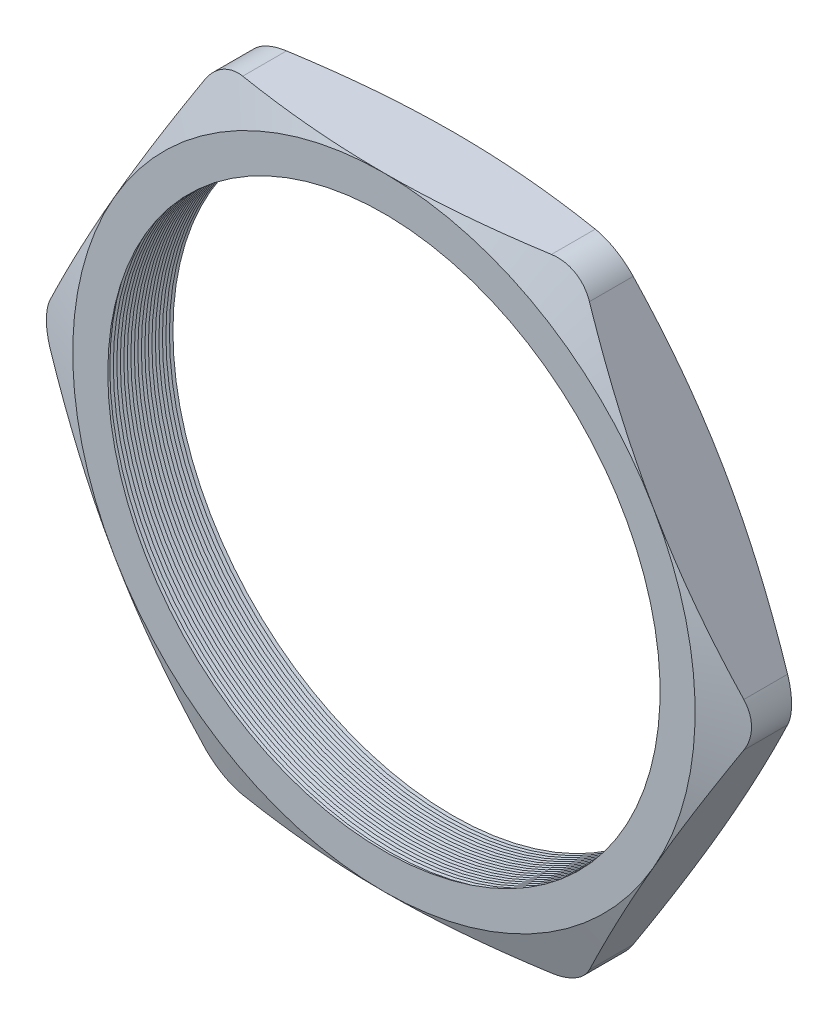
SolidWorks part; units mm, degrees
ref_plane "Front Plane" through (0, 0, 0) normal (0, 0, 1) x (1, 0, 0)
ref_plane "Top Plane" through (0, 0, 0) normal (0, 1, 0) x (1, 0, 0)
ref_plane "Right Plane" through (0, 0, 0) normal (1, 0, 0) x (0, 0, -1)
sketch "Sketch1" plane through (0, 0, 0) normal (0, 0, 1) x (1, 0, 0)
  line L1 (-20.8239, 0) -> (-10.4119, -18.034)
  line L2 (-10.4119, -18.034) -> (10.4119, -18.034)
  line L3 (10.4119, -18.034) -> (20.8239, 0)
  line L4 (20.8239, 0) -> (10.4119, 18.034)
  line L5 (10.4119, 18.034) -> (-10.4119, 18.034)
  line L6 (-10.4119, 18.034) -> (-20.8239, 0)
  circle A0 centre (0, 0) radius 18.034 construction
  circle A1 centre (0, 0) radius 16.002
  dimension "TS" = 32.004
  dimension "H" = 36.068
extrude "Extrude1" add sketch "Sketch1" along normal blind 4.064
fillet "Fillet1" radius 2.54 6 edges at (-10.4119, 18.034, 2.032) (-20.8239, 0, 2.032) (-10.4119, -18.034, 2.032) (10.4119, -18.034, 2.032) (20.8239, 0, 2.032) (10.4119, 18.034, 2.032)
sketch "Sketch2" plane through (0, 0, 4.064) normal (0, 0, 1) x (1, 0, 0)
  line L0 (8.9455, 18.034) -> (-8.9455, 18.034) construction
  circle A0 centre (0, 0) radius 18.034
extrude "Cut-Extrude1" cut sketch "Sketch2" against normal through all draft 70 flip side to cut
sketch "Sketch3" plane through (0, 0, 0) normal (0, 0, -1) x (-1, 0, 0)
  circle A0 centre (0, 0) radius 18.034
extrude "Cut-Extrude2" cut sketch "Sketch3" against normal through all draft 70 flip side to cut
sketch "Sketch4" plane through (0, 0, 0) normal (0, 1, 0) x (1, 0, 0)
  line L0 (-16.002, -4.064) -> (-16.002, -3.6241)
  line L2 (-16.002, -3.6241) -> (-16.383, -3.844)
  line L3 (-16.383, -3.844) -> (-16.002, -4.064)
  line L5 (-16.002, 0) -> (-16.002, -4.064) construction
  line L6 (-16.002, -4.064) -> (16.002, -4.064) construction
  dimension "D1" = 60
  dimension "D2" = 60
  dimension "D3" = 0.381
revolve "Cut-Revolve1" cut sketch "Sketch4" angle 360 about axis through (0, 0, 4.064) along (0, 0, -1)
pattern_linear "LPattern1" count 20 spacing 0.2032 along (0, 0, -1) of "Cut-Revolve1"
